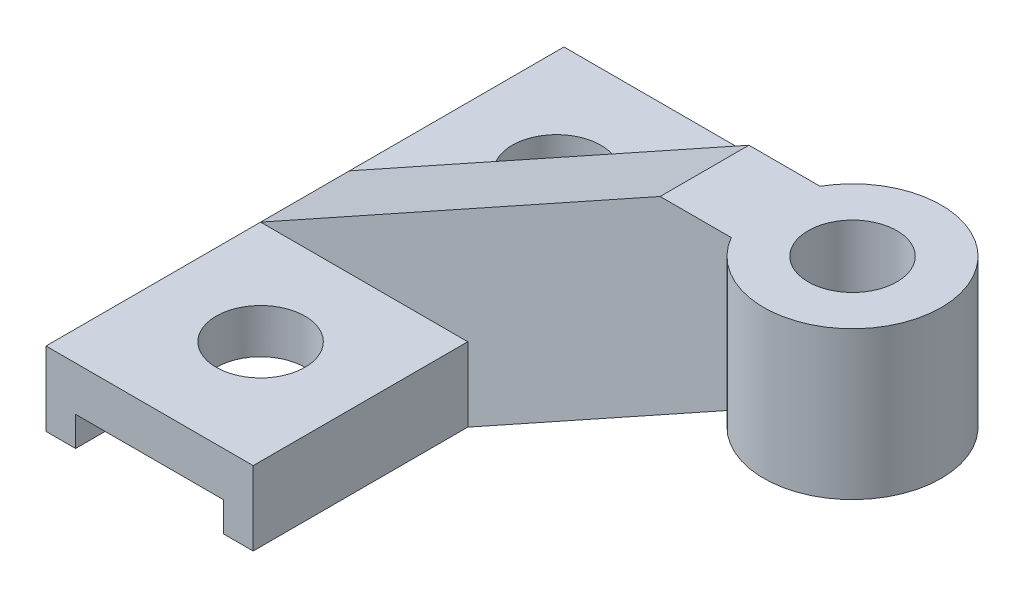
SolidWorks part; units mm, degrees
ref_plane "前基準面" through (0, 0, 0) normal (0, 0, 1) x (1, 0, 0)
ref_plane "上基準面" through (0, 0, 0) normal (0, 1, 0) x (1, 0, 0)
ref_plane "右基準面" through (0, 0, 0) normal (1, 0, 0) x (0, 0, -1)
sketch "草圖1" plane through (0, 0, 0) normal (0, 0, 1) x (1, 0, 0)
  line L0 (-7, 0) -> (7, 0)
  line L1 (7, 0) -> (7, -5)
  line L2 (7, -5) -> (5, -5)
  line L3 (5, -5) -> (5, -3)
  line L4 (5, -3) -> (-5, -3)
  line L5 (-5, -3) -> (-5, -5)
  line L6 (-5, -5) -> (-7, -5)
  line L7 (-7, -5) -> (-7, 0)
  point P7 (0, 0)
  point P10 (0, -3)
  dimension "D1" = 2
  dimension "D2" = 10
  dimension "D3" = 5
  dimension "D4" = 14
extrude "填料-伸長1" add sketch "草圖1" along normal mid plane 35
sketch "草圖4" plane through (0, 0, 0) normal (0, 0, 1) x (1, 0, 0)
  line L0 (-7, 0) -> (20, 15)
  line L1 (20, 15) -> (25, 15)
  line L2 (25, 15) -> (25, 5)
  line L3 (25, 5) -> (7, -5)
  line L4 (5, -5) -> (7, -5) construction
  line L5 (-7, 0) -> (7, 0)
  line L6 (7, 0) -> (7, -5)
  dimension "D1" = 10
  dimension "D2" = 27
  dimension "D3" = 20
extrude "填料-伸長2" add sketch "草圖4" along normal mid plane 6
sketch "草圖5" plane through (0, 0, 0) normal (0, 1, 0) x (1, 0, 0)
  circle A0 centre (30, 0) radius 6
  circle A1 centre (30, 0) radius 3
  dimension "D1" = 6
  dimension "D2" = 12
  dimension "D3" = 30
extrude "填料-伸長3" add sketch "草圖5" along normal blind 10 from offset 5
sketch "草圖2" plane through (0, 0, 0) normal (0, 1, 0) x (1, 0, 0)
  line L0 (-14.2998, 0) -> (11.5141, 0) construction
  circle A0 centre (0, -10) radius 3
  circle A1 centre (0, 10) radius 3
  dimension "D1" = 10
  dimension "D2" = 6
extrude "除料-伸長1" cut sketch "草圖2" against normal through all
